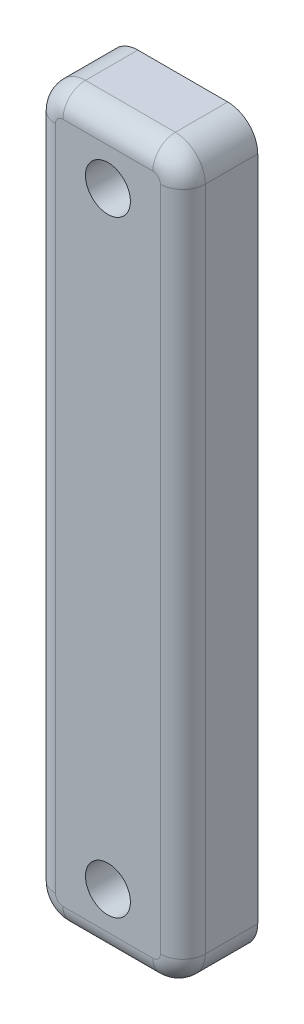
SolidWorks part; units mm, degrees
ref_plane "Front Plane" through (0, 0, 0) normal (0, 0, 1) x (1, 0, 0)
ref_plane "Top Plane" through (0, 0, 0) normal (0, 1, 0) x (1, 0, 0)
ref_plane "Right Plane" through (0, 0, 0) normal (1, 0, 0) x (0, 0, -1)
sketch "Sketch2" plane through (0, 0, 0) normal (0, 0, 1) x (1, 0, 0)
  line L4 (10, 7.5842) -> (10, 18.5842)
  line L5 (8, 20.5842) -> (2, 20.5842)
  line L6 (0, 18.5842) -> (0, 7.5842)
  line L7 (0, 7.5842) -> (10, 7.5842)
  line L9 (8, 20.5842) -> (2, 20.5842)
  line L12 (10, -25.9158) -> (10, -14.9158)
  line L13 (10, -14.9158) -> (0, -14.9158)
  line L14 (0, -14.9158) -> (0, -25.9158)
  line L15 (2, -27.9158) -> (8, -27.9158)
  line L16 (10, -25.9158) -> (10, 18.5842)
  line L18 (0, 18.5842) -> (0, -25.9158)
  line L19 (2, -27.9158) -> (8, -27.9158)
  arc A2 (10, 18.5842) -> (8, 20.5842) centre (8, 18.5842) ccw
  arc A3 (2, 20.5842) -> (0, 18.5842) centre (2, 18.5842) ccw
  arc A4 (10, 18.5842) -> (8, 20.5842) centre (8, 18.5842) ccw
  arc A5 (2, 20.5842) -> (0, 18.5842) centre (2, 18.5842) ccw
  arc A6 (0, -25.9158) -> (2, -27.9158) centre (2, -25.9158) ccw
  arc A7 (8, -27.9158) -> (10, -25.9158) centre (8, -25.9158) ccw
  arc A8 (0, -25.9158) -> (2, -27.9158) centre (2, -25.9158) ccw
  arc A9 (8, -27.9158) -> (10, -25.9158) centre (8, -25.9158) ccw
  dimension "D1" = 0
  dimension "D2" = 0
extrude "Boss-Extrude1" add sketch "Sketch2" along normal blind 5
sketch "Sketch4" plane through (0, 0, 0) normal (0, 0, -1) x (-1, 0, 0)
  circle A0 centre (-5, -23.9158) radius 1.5
  circle A1 centre (-5, 16.5842) radius 1.5
extrude "Cut-Extrude1" cut sketch "Sketch4" against normal through all
fillet "Fillet1" radius 1.5 8 edges at (9.4142, -27.33, 5) (5, -27.9158, 5) (0.5858, -27.33, 5) (0, -3.6658, 5) (0.5858, 19.9984, 5) (5, 20.5842, 5) (9.4142, 19.9984, 5) (10, -3.6658, 5)
